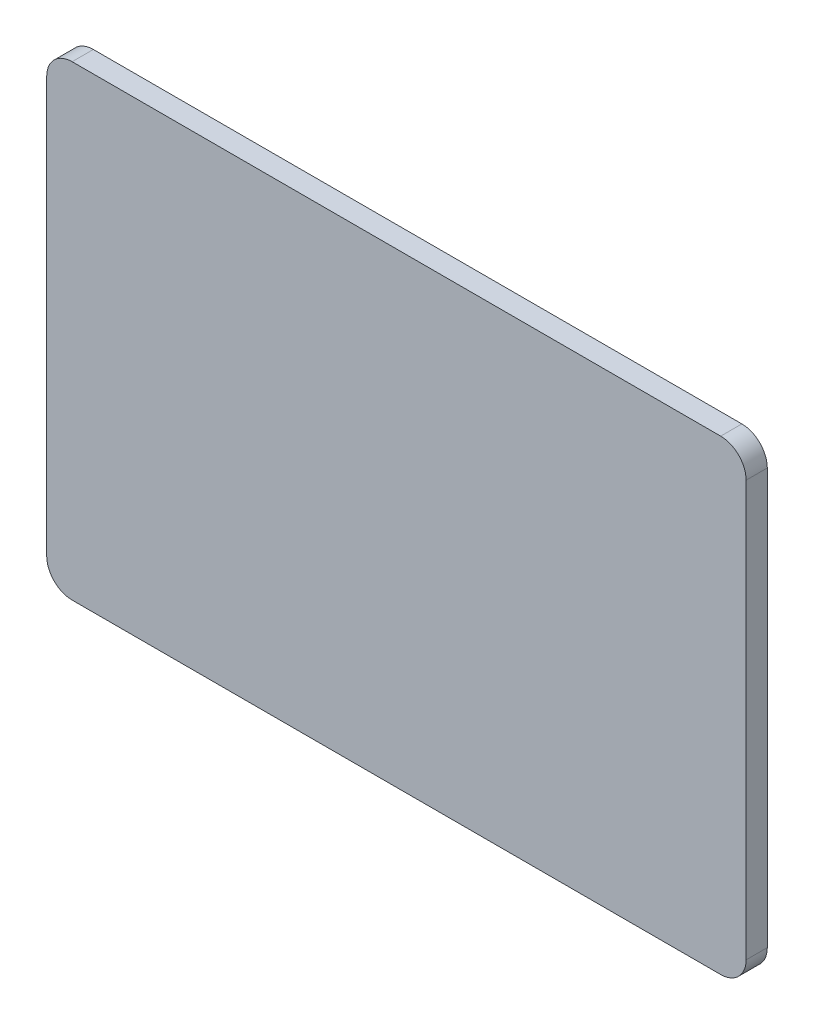
SolidWorks part; units mm, degrees
ref_plane "Front Plane" through (0, 0, 0) normal (0, 0, 1) x (1, 0, 0)
ref_plane "Top Plane" through (0, 0, 0) normal (0, 1, 0) x (1, 0, 0)
ref_plane "Right Plane" through (0, 0, 0) normal (1, 0, 0) x (0, 0, -1)
sketch "Sketch1" plane through (0, 0, 0) normal (0, 0, 1) x (1, 0, 0)
  line L1 (0, 0) -> (825, 0)
  line L2 (0, 0) -> (0, 550)
  line L3 (0, 550) -> (825, 550)
  line L4 (825, 0) -> (825, 550)
  dimension "D1" = 825
  dimension "D2" = 550
extrude "Boss-Extrude1" add sketch "Sketch1" along normal blind 25
fillet "Fillet1" radius 30 1 edges at (0, 550, 12.5)
fillet "Fillet2" radius 30 1 edges at (825, 550, 12.5)
fillet "Fillet3" radius 30 1 edges at (0, 0, 12.5)
fillet "Fillet4" radius 30 1 edges at (825, 0, 12.5)
